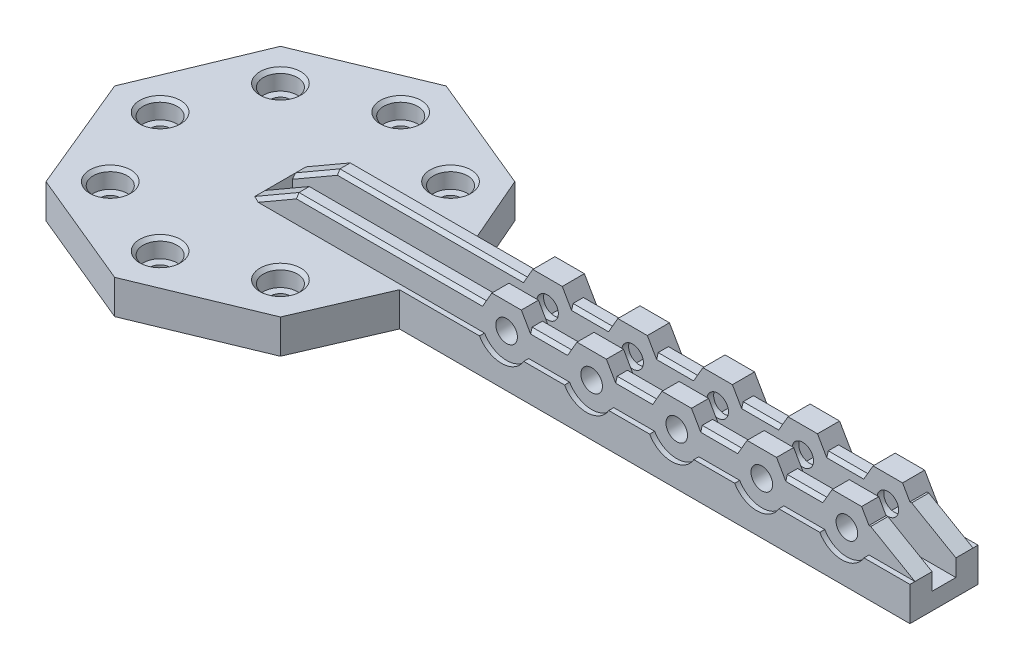
SolidWorks part; units mm, degrees
ref_plane "Front Plane" through (0, 0, 0) normal (0, 0, 1) x (1, 0, 0)
ref_plane "Top Plane" through (0, 0, 0) normal (0, 1, 0) x (1, 0, 0)
ref_plane "Right Plane" through (0, 0, 0) normal (1, 0, 0) x (0, 0, -1)
sketch "Sketch1" plane through (0, 0, 0) normal (0, 1, 0) x (1, 0, 0)
  line L1 (48.7076, 0) -> (34.4415, 34.4415)
  line L2 (34.4415, 34.4415) -> (0, 48.7076)
  line L3 (0, 48.7076) -> (-34.4415, 34.4415)
  line L4 (-34.4415, 34.4415) -> (-48.7076, 0)
  line L5 (-48.7076, 0) -> (-34.4415, -34.4415)
  line L6 (-34.4415, -34.4415) -> (0, -48.7076)
  line L7 (0, -48.7076) -> (34.4415, -34.4415)
  line L8 (34.4415, -34.4415) -> (48.7076, 0)
  circle A0 centre (0, 0) radius 45 construction
  dimension "D1" = 90
extrude "Boss-Extrude1" add sketch "Sketch1" against normal blind 10
sketch "Sketch4" plane through (0, 0, 0) normal (0, 1, 0) x (1, 0, 0)
  line L1 (0, 0) -> (-45, -18.6396) construction
  line L3 (0, 0) -> (63.6396, 0) construction
  circle A0 centre (0, 0) radius 45 construction
  point P3 (0, 0)
  point P4 (0, 0)
  point P5 (0, 0)
  point P7 (0, 0)
sketch "Sketch2" plane through (0, 0, 0) normal (0, 1, 0) x (1, 0, 0)
  circle A0 centre (-35.3553, 0) radius 2.85
  circle A1 centre (-25, 25) radius 2.85
  circle A2 centre (0, 35.3553) radius 2.85
  circle A3 centre (25, 25) radius 2.85
  circle A5 centre (25, -25) radius 2.85
  circle A6 centre (0, -35.3553) radius 2.85
  circle A7 centre (-25, -25) radius 2.85
  circle A8 centre (35.3553, 0) radius 2.85 [skipped]
  point P2 (0, 0)
  point P20 (0, 0)
  dimension "D3" = 5.7
  dimension "D1" = 50
  dimension "D2" = 8
extrude "Cut-Extrude1" cut sketch "Sketch2" against normal blind 14
sketch "Sketch5" plane through (0, 0, 0) normal (0, 1, 0) x (1, 0, 0)
  circle A0 centre (-35.3553, 0) radius 5
  circle A1 centre (-25, 25) radius 5
  circle A2 centre (0, 35.3553) radius 5
  circle A3 centre (25, 25) radius 5
  circle A5 centre (25, -25) radius 5
  circle A6 centre (0, -35.3553) radius 5
  circle A7 centre (-25, -25) radius 5
  circle A8 centre (35.3553, 0) radius 5 [skipped]
  point P19 (0, 0)
  point P21 (0, 0)
  point P22 (0, 0)
  point P23 (0, 0)
  point P24 (0, 0)
  point P25 (0, 0)
  point P26 (0, 0)
  point P27 (0, 0)
  dimension "D1" = 10
  dimension "D2" = 8
extrude "Cut-Extrude2" cut sketch "Sketch5" against normal blind 5.5
sketch "Sketch7" plane through (0, 0, 0) normal (0, 1, 0) x (1, 0, 0)
  line L0 (45, -10) -> (34.4415, -34.4415)
  line L1 (45, 10) -> (195, 10)
  line L2 (45, 10) -> (45, -10) construction
  line L3 (45, -10) -> (195, -10)
  line L4 (195, 10) -> (195, -10)
  line L5 (34.4415, -34.4415) -> (34.4415, 34.4415)
  line L6 (34.4415, 34.4415) -> (45, 10)
  circle A0 centre (0, 0) radius 45 construction
  point P6 (195, 0)
  dimension "D1" = 150
  dimension "D2" = 20
extrude "Boss-Extrude3" add sketch "Sketch7" against normal blind 10
sketch "Sketch8" plane through (0, 0, 0) normal (0, 1, 0) x (1, 0, 0)
  line L0 (45, -10) -> (195, -10) construction
  line L1 (0, -3.5) -> (195, -3.5)
  line L2 (0, -3.5) -> (0, -8.53)
  line L3 (0, -8.53) -> (195, -8.53)
  line L4 (195, -3.5) -> (195, -8.53)
  line L6 (195, -10) -> (195, 10) construction
  line L7 (-5.5, 0) -> (5.5, 0) construction
  line L8 (0, 8.53) -> (195, 8.53)
  line L9 (195, 3.5) -> (195, 8.53)
  line L10 (0, 3.5) -> (195, 3.5)
  line L11 (0, 3.5) -> (0, 8.53)
  dimension "D1" = 3.5
  dimension "D2" = 1.47
ref_plane "Plane1" through (0, 0.5, 0) normal (0, 1, 0) x (1, 0, 0)
extrude "Boss-Extrude4" add sketch "Sketch8" along normal blind 7.5
sketch "Sketch13" plane through (0, 0, -8.53) normal (0, 0, -1) x (-1, 0, 0)
  line L0 (-195, 0) -> (-45, 0) construction
  line L1 (-170.6699, -3.75) -> (-166.3397, 3.75) construction
  line L2 (-166.3397, 3.75) -> (-170.6699, 11.25)
  line L3 (-170.6699, 11.25) -> (-179.3301, 11.25)
  line L4 (-179.3301, 11.25) -> (-183.6603, 3.75)
  line L5 (-183.6603, 3.75) -> (-179.3301, -3.75) construction
  line L6 (-179.3301, -3.75) -> (-170.6699, -3.75) construction
  line L7 (-183.6603, 3.75) -> (-183.6603, -3.75)
  line L8 (-195, 7.5) -> (0, 7.5) construction
  line L9 (-168.9378, 3.75) -> (-171.9689, 9)
  line L10 (-171.9689, 9) -> (-178.0311, 9)
  line L11 (-178.0311, 9) -> (-181.0622, 3.75)
  line L12 (-181.0622, 3.75) -> (-178.0311, -1.5)
  line L13 (-178.0311, -1.5) -> (-171.9689, -1.5)
  line L14 (-171.9689, -1.5) -> (-168.9378, 3.75)
  line L15 (-183.6603, -3.75) -> (-166.3397, -3.75)
  line L16 (-166.3397, -3.75) -> (-166.3397, 3.75)
  circle A0 centre (-175, 3.75) radius 7.5 construction
  circle A1 centre (-175, 3.75) radius 5.25 construction
  dimension "D1" = 15
  dimension "D2" = 175
  dimension "D3" = 3.75
  dimension "D4" = 10.5
extrude "Boss-Extrude5" add sketch "Sketch13" along normal up to surface and the other way up to surface
sketch "Sketch9" plane through (0, 0, 8.53) normal (0, 0, 1) x (1, 0, 0)
  line L0 (0, 0) -> (12.9904, 7.5)
  line L1 (0, 7.5) -> (195, 7.5) construction
  line L2 (0, 7.5) -> (12.9904, 7.5)
  line L3 (182.0096, 7.5) -> (195, 0)
  line L4 (195, 0) -> (195, 7.5)
  line L5 (195, 7.5) -> (182.0096, 7.5)
  line L6 (0, 0) -> (0, 7.5)
  dimension "D1" = 60
  dimension "D2" = 60
extrude "Cut-Extrude3" cut sketch "Sketch9" against normal up to surface (17.06 mm away) up to face at (100.2369, 3.75, -8.53)
sketch "Sketch10" plane through (0, 0, 0) normal (0, 1, 0) x (1, 0, 0)
  line L1 (195, -3.5) -> (0, -3.5)
  line L2 (195, -3.5) -> (195, 3.5)
  line L3 (195, 3.5) -> (0, 3.5)
  line L4 (0, -3.5) -> (0, 3.5)
  dimension "D1" = 7
extrude "Cut-Extrude4" cut sketch "Sketch10" against normal blind 5
sketch "Sketch11" plane through (0, 0, 8.53) normal (0, 0, 1) x (1, 0, 0)
  circle A0 centre (175, 3.75) radius 3.175
  dimension "D1" = 175
  dimension "D3" = 6.35
  dimension "D2" = 3.75
extrude "Cut-Extrude5" cut sketch "Sketch11" against normal blind 23
sketch "Sketch12" plane through (0, 0, 10) normal (0, 0, 1) x (1, 0, 0)
  circle A0 centre (175, 3.75) radius 7.5
  dimension "D1" = 15
extrude "Cut-Extrude6" cut sketch "Sketch12" against normal up to surface (1.47 mm away) up to face at (178.175, 3.75, 8.53)
sketch "Sketch14" plane through (0, 7.5, 0) normal (0, 1, 0) x (1, 0, 0)
  line L4 (171.1029, 3.5) -> (178.8971, 3.5)
  line L5 (178.8971, 3.5) -> (178.8971, 8.53)
  line L6 (178.8971, 8.53) -> (171.1029, 8.53)
  line L8 (171.1029, 3.5) -> (178.8971, 3.5)
  line L10 (178.8971, 8.53) -> (171.1029, 8.53)
  line L12 (178.8971, 3.5) -> (178.8971, 8.53)
  line L14 (171.1029, 8.53) -> (171.1029, 3.5)
  line L15 (171.1029, 8.53) -> (171.1029, 3.5)
  dimension "D1" = 0
extrude "Boss-Extrude6" add sketch "Sketch14" along normal up to surface (1.5 mm away) up to face at (175, 9, -6.75)
sketch "Sketch15" plane through (0, 0, -10) normal (0, 0, -1) x (-1, 0, 0)
  line L1 (-168.9378, 3.75) -> (-171.9689, 9)
  line L2 (-171.9689, 9) -> (-178.0311, 9)
  line L3 (-178.0311, 9) -> (-181.0622, 3.75)
  line L4 (-181.0622, 3.75) -> (-178.0311, -1.5)
  line L5 (-178.0311, -1.5) -> (-171.9689, -1.5)
  line L6 (-171.9689, -1.5) -> (-168.9378, 3.75)
  circle A0 centre (-175, 3.75) radius 5.25 construction
extrude "Cut-Extrude7" cut sketch "Sketch15" against normal offset from surface (4.5 mm away) 2 up to face at (171.825, 3.75, -3.5)
sketch "Sketch16" plane through (0, 0, 8.53) normal (0, 0, 1) x (1, 0, 0)
  line L0 (168.5048, 7.5) -> (170.6699, 11.25)
  line L1 (170.6699, 11.25) -> (179.3301, 11.25)
  line L2 (179.3301, 11.25) -> (181.4952, 7.5)
  line L3 (181.4952, 7.5) -> (168.5048, 7.5)
extrude "Boss-Extrude7" add sketch "Sketch16" against normal up to surface (5.03 mm away) up to face at (178.175, 3.75, 3.5)
pattern_linear "LPattern4" count 5 spacing 25 along (-1, 0, 0) of "Boss-Extrude5", "Cut-Extrude5", "Cut-Extrude6", "Boss-Extrude6", "Cut-Extrude7", "Boss-Extrude7"
chamfer "Chamfer1" distance 1 angle 45 7 edges at (25, 0, -20) (0, 0, -30.3553) (-25, 0, -20) (-35.3553, 0, 5) (-25, 0, 30) (0, 0, 40.3553) (25, 0, 30)
chamfer "Chamfer2" distance 1 angle 45 24 edges at (162.5, 7.5, -3.5) (162.5, 7.5, -8.53) (137.5, 7.5, -3.5) (137.5, 7.5, -8.53) (112.5, 7.5, -3.5) (112.5, 7.5, -8.53) (87.5, 7.5, -3.5) (87.5, 7.5, -8.53) (40.7476, 7.5, -3.5) (6.4952, 3.75, -3.5) (40.7476, 7.5, -8.53) (6.4952, 3.75, -8.53) (137.5, 7.5, 8.53) (137.5, 7.5, 3.5) (162.5, 7.5, 8.53) (162.5, 7.5, 3.5) (6.4952, 3.75, 3.5) (40.7476, 7.5, 3.5) (6.4952, 3.75, 8.53) (40.7476, 7.5, 8.53) (87.5, 7.5, 3.5) (87.5, 7.5, 8.53) (112.5, 7.5, 3.5) (112.5, 7.5, 8.53)
